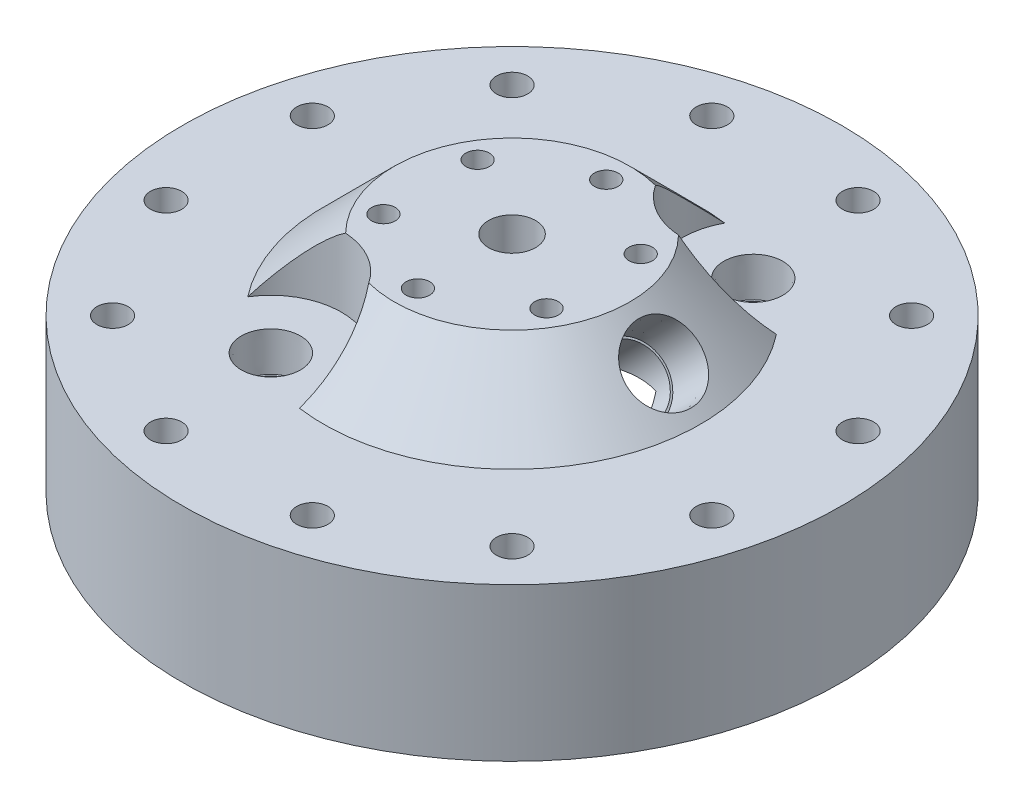
SolidWorks part; units mm, degrees
ref_plane "Front Plane" through (0, 0, 0) normal (0, 0, 1) x (1, 0, 0)
ref_plane "Top Plane" through (0, 0, 0) normal (0, 1, 0) x (1, 0, 0)
ref_plane "Right Plane" through (0, 0, 0) normal (1, 0, 0) x (0, 0, -1)
sketch "Sketch1" plane through (0, 0, 0) normal (0, 0, 1) x (1, 0, 0)
  line L0 (0, 0) -> (0, 51.199) construction
  line L2 (-88.9, 0) -> (-88.9, 41.275)
  line L3 (-88.9, 41.275) -> (-50.8, 41.275)
  line L4 (-50.8, 41.275) -> (-31.75, 60.325)
  line L5 (-31.75, 60.325) -> (0, 60.325)
  line L6 (0, 60.325) -> (0, 34.925)
  line L8 (-31.75, 34.925) -> (0, 34.925)
  line L12 (-31.75, 34.925) -> (-31.75, 22.225)
  line L15 (-31.75, 22.225) -> (-50.8, 22.225)
  line L16 (-50.8, 22.225) -> (-50.8, 3.175)
  line L17 (-50.8, 3.175) -> (-52.3875, 3.175)
  line L18 (-52.3875, 3.175) -> (-52.3875, 5.715)
  line L19 (-52.3875, 5.715) -> (-55.9435, 5.715)
  line L20 (-55.9435, 5.715) -> (-55.9435, 3.175)
  line L21 (-88.9, 0) -> (-57.15, 0)
  line L23 (-55.9435, 3.175) -> (-57.15, 3.175)
  line L24 (-57.15, 3.175) -> (-57.15, 0)
  dimension "D1" = 6.35
  dimension "D2" = 31.75
  dimension "D3" = 19.05
  dimension "D4" = 31.75
  dimension "D5" = 88.9
  dimension "D6" = 12.7
  dimension "D7" = 135
  dimension "D8" = 3.175
  dimension "D9" = 22.225
  dimension "D10" = 41.275
  dimension "D11" = 6.35
  dimension "D12" = 50.8
  dimension "D13" = 3.556
  dimension "D14" = 2.54
  dimension "D15" = 1.5875
revolve "Revolve1" add sketch "Sketch1" angle 360 about L0
hole_wizard "5/16 Clearance Hole1" positions "Sketch4" profile "Sketch6" hole size "5/16" standard "ANSI Inch" end condition through all
sketch "Sketch4" plane through (0, 41.275, 0) normal (0, 1, 0) x (1, 0, 0)
  line L0 (-73.6035, -19.722) -> (0, 0) construction
  line L2 (0, 0) -> (-63.9148, 0) construction
  point P0 (-73.6035, -19.722)
  dimension "D1" = 76.2
  dimension "D2" = 15
sketch "Sketch6" plane through (-73.6035, 41.275, 19.722) normal (1, 0, 0) x (0, 0, 1)
  line L0 (0, 0) -> (0, 41.275)
  line L1 (0, 41.275) -> (4.2164, 41.275)
  line L2 (4.2164, 41.275) -> (4.2164, 0)
  line L5 (4.2164, 0) -> (0, 0)
  line L11 (0, -6.35) -> (0, 107.95) construction
  dimension "Thru Hole Dia." = 8.4328
  dimension "Thru Hole Depth" = 41.275
pattern_circular "CirPattern1" count 12 over 360 about axis through (0, 0, 0) along (0, 1, 0) of "5/16 Clearance Hole1"
hole_wizard "1/2 (0.5) Diameter Hole1" positions "Sketch7" profile "Sketch8" hole size "1/2" standard "ANSI Inch" end condition through all
sketch "Sketch7" plane through (0, 60.325, 0) normal (0, 1, 0) x (1, 0, 0)
  point P0 (0, 0)
sketch "Sketch8" plane through (0, 60.325, 0) normal (1, 0, 0) x (0, 0, 1)
  line L0 (0, 0) -> (0, 60.325)
  line L1 (0, 60.325) -> (6.35, 60.325)
  line L2 (6.35, 60.325) -> (6.35, 0)
  line L5 (6.35, 0) -> (0, 0)
  line L11 (0, -6.35) -> (0, 107.95) construction
  dimension "Thru Hole Dia." = 12.7
  dimension "Thru Hole Depth" = 60.325
ref_plane "Plane1" through (46.0375, 46.0375, 0) normal (0.7071, 0.7071, 0) x (0, 0, -1)
sketch "Sketch9" plane through (46.0375, 46.0375, 0) normal (0.7071, 0.7071, 0) x (0, 0, -1)
  line L0 (0, -6.7352) -> (0, 20.2056) construction
  ellipse E0 centre (0, 29.1858) end of major axis (-50.8, 29.1858) minor radius 35.921 construction
  ellipse E1 centre (0, 42.6562) end of major axis (-31.75, 42.6562) minor radius 22.4506 construction
  point P15 (0, 6.7352)
hole_wizard "1/2 NPT Tapped Hole1" positions "Sketch10" profile "Sketch11" size "1/2" standard "ANSI Inch" end condition through all
sketch "Sketch10" plane through (46.0375, 46.0375, 0) normal (0.7071, 0.7071, 0) x (0, 0, -1)
  point P0 (0, 6.7352)
sketch "Sketch11" plane through (41.275, 50.8, 0) normal (0, 0, 1) x (-0.7071, 0.7071, 0)
  line L0 (0, 0) -> (0, 127.9686)
  line L1 (0, 127.9686) -> (8.9281, 127.9686)
  line L2 (-9.4797, 13.462) -> (-9.8828, 0) construction
  line L3 (8.9281, 127.9686) -> (8.9281, 13.462)
  line L4 (8.9281, 13.462) -> (9.4797, 13.462)
  line L5 (9.4797, 13.462) -> (9.8828, 0)
  line L7 (9.8828, 0) -> (0, 0)
  line L8 (0, -6.35) -> (0, 107.95) construction
  line L11 (-8.9281, 13.462) -> (-9.4797, 13.462) construction
  dimension "Thru Tap Drill Dia." = 17.8562
  dimension "Thru Tap Drill Depth" = 127.9686
  dimension "Thread Dia." = 19.7656
  dimension "Thread Angle" = 3.43
  dimension "Thread Depth" = 13.462
cosmetic thread "Hole Thread3" parameters "D1"=13.462, "D2"=36.8399
hole_wizard "1 (1.5) Diameter Hole1" positions "Sketch14" profile "Sketch16" hole size "1" standard "ANSI Inch"
sketch "Sketch14" plane through (0, 60.325, 0) normal (0, 1, 0) x (1, 0, 0)
  line L0 (-23.8125, -41.2445) -> (0, 0) construction
  line L2 (0, 0) -> (-62.2091, 0) construction
  point P0 (-23.8125, -41.2445)
  dimension "D1" = 47.625
  dimension "D2" = 60
sketch "Sketch16" plane through (-23.8125, 60.325, 41.2445) normal (1, 0, 0) x (0, 0, 1)
  line L0 (0, 0) -> (0, 30.4964)
  line L1 (0, 30.4964) -> (19.05, 19.05)
  line L2 (19.05, 19.05) -> (19.05, 0)
  line L5 (19.05, 0) -> (0, 0)
  line L10 (0, 30.4964) -> (-19.05, 19.05) construction
  line L11 (0, -6.35) -> (0, 107.95) construction
  dimension "Hole Dia." = 38.1
  dimension "Hole Depth" = 19.05
  dimension "Drill Angle" = 118
hole_wizard "3/8 NPT Tapped Hole1" positions "Sketch17" profile "Sketch19" size "3/8" standard "ANSI Inch"
sketch "Sketch17" plane through (0, 41.275, 0) normal (0, 1, 0) x (1, 0, 0)
  line L0 (0, 0) -> (-55.2485, 0) construction
  line L2 (0, 0) -> (-23.8125, -41.2445) construction
  point P0 (-23.8125, -41.2445)
  dimension "D1" = 47.625
  dimension "D2" = 60
cosmetic thread "Hole Thread4" parameters "D1"=10.414, "D2"=17.1495
sketch "Sketch19" plane through (-23.8125, 41.275, 41.2445) normal (1, 0, 0) x (0, 0, 1)
  line L0 (0, 0) -> (0, 26.6406)
  line L1 (7.1374, 22.352) -> (0, 26.6406)
  line L2 (-7.1374, 22.352) -> (0, 26.6406) construction
  line L3 (7.1374, 22.352) -> (7.1374, 10.414)
  line L4 (7.1374, 10.414) -> (7.6537, 10.414)
  line L5 (7.6537, 10.414) -> (7.9655, 0)
  line L6 (-7.6537, 10.414) -> (-7.9655, 0) construction
  line L7 (7.9655, 0) -> (0, 0)
  line L8 (0, -6.35) -> (0, 107.95) construction
  line L11 (-7.1374, 10.414) -> (-7.6537, 10.414) construction
  dimension "Tap Drill Dia." = 14.2748
  dimension "Tap Drill Depth" = 22.352
  dimension "Thread Dia." = 15.9311
  dimension "Thread Angle" = 3.43
  dimension "Thread Depth" = 10.414
  dimension "Drill Angle" = 118
hole_wizard "1/4 (0.25) Diameter Hole1" positions "Sketch20" profile "Sketch21" hole size "1/4" standard "ANSI Inch"
sketch "Sketch20" plane through (0, 60.325, 0) normal (0, 1, 0) x (1, 0, 0)
  line L0 (0, 0) -> (21.997, 12.7) construction
  line L2 (0, 0) -> (14.3987, 0) construction
  point P0 (21.997, 12.7)
  dimension "D1" = 25.4
  dimension "D2" = 30
sketch "Sketch21" plane through (21.997, 60.325, -12.7) normal (1, 0, 0) x (0, 0, 1)
  line L0 (0, 0) -> (0, 17.7827)
  line L1 (0, 17.7827) -> (3.175, 15.875)
  line L2 (3.175, 15.875) -> (3.175, 0)
  line L5 (3.175, 0) -> (0, 0)
  line L10 (0, 17.7827) -> (-3.175, 15.875) construction
  line L11 (0, -6.35) -> (0, 107.95) construction
  dimension "Hole Dia." = 6.35
  dimension "Hole Depth" = 15.875
  dimension "Drill Angle" = 118
pattern_circular "CirPattern2" count 6 over 360 about axis through (0, 0, 0) along (0, 1, 0) of "1/4 (0.25) Diameter Hole1"
pattern_circular "CirPattern3" count 2 over 360 about axis through (0, 0, 0) along (0, 1, 0) of "1 (1.5) Diameter Hole1", "3/8 NPT Tapped Hole1"
cosmetic thread "Hole Thread5" parameters "D1"=10.414, "D2"=17.1495
hole_wizard "1/8 (0.125) Diameter Hole1" positions "Sketch22" profile "Sketch24" hole size "1/8" standard "ANSI Inch"
sketch "Sketch22" plane through (0, 22.225, 0) normal (0, -1, 0) x (-1, 0, 0)
  line L0 (0, 0) -> (-23.8125, 41.2445) construction
  line L2 (0, 0) -> (0, 44.45) construction
  point P0 (0, 44.45)
  dimension "D1" = 30
  dimension "D2" = 44.45
sketch "Sketch24" plane through (0, 22.225, -44.45) normal (1, 0, 0) x (0, 0, -1)
  line L0 (0, 0) -> (0, 7.3039)
  line L1 (0, 7.3039) -> (1.5875, 6.35)
  line L2 (1.5875, 6.35) -> (1.5875, 0)
  line L5 (1.5875, 0) -> (0, 0)
  line L10 (0, 7.3039) -> (-1.5875, 6.35) construction
  line L11 (0, -6.35) -> (0, 107.95) construction
  dimension "Hole Dia." = 3.175
  dimension "Hole Depth" = 6.35
  dimension "Drill Angle" = 118
